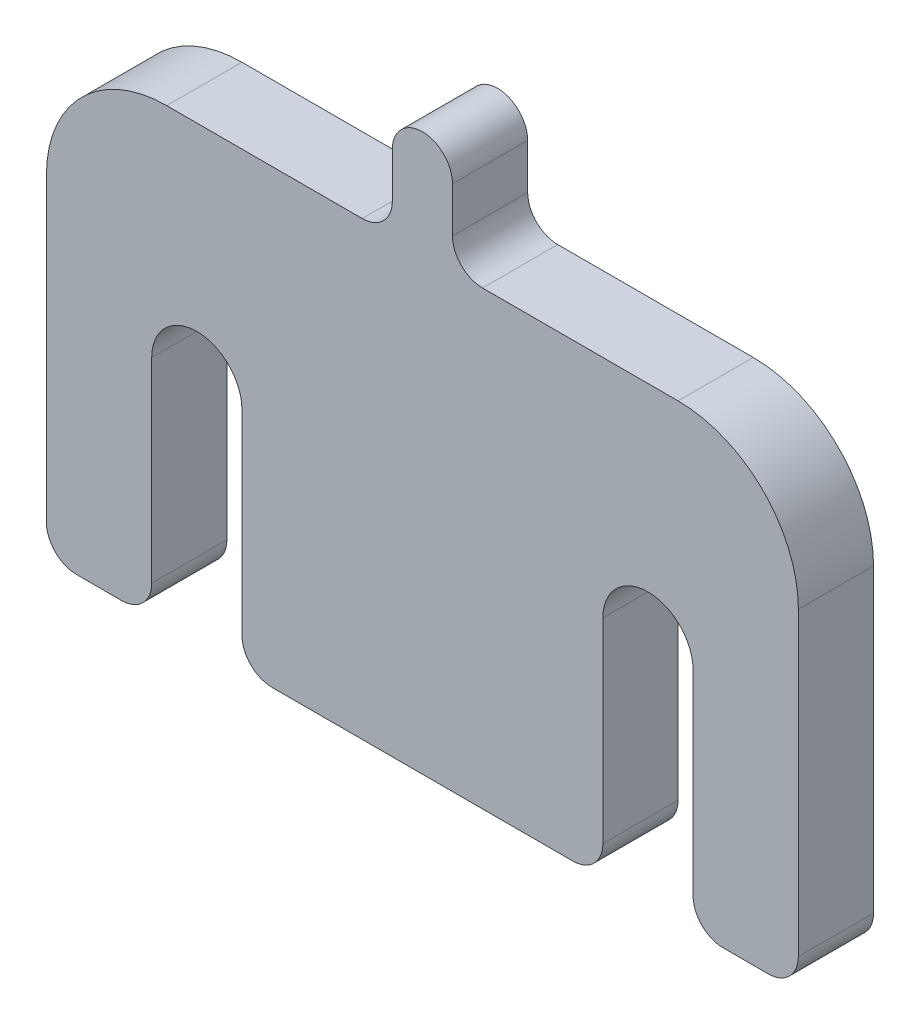
SolidWorks part; units mm, degrees
material "7075-O (SS)"
ref_plane "Płaszczyzna XY" through (0, 0, 0) normal (0, 0, 1) x (1, 0, 0)
ref_plane "Płaszczyzna XZ" through (0, 0, 0) normal (0, 1, 0) x (1, 0, 0)
ref_plane "Płaszczyzna YZ" through (0, 0, 0) normal (1, 0, 0) x (0, 0, -1)
sketch "Szkic1" plane through (0, 0, 0) normal (0, 0, 1) x (1, 0, 0)
  line L0 (15, 0) -> (-15, 0) construction
  line L1 (18, 0) -> (18, -15)
  line L2 (25, -15) -> (-25, -15)
  line L3 (25, -15) -> (25, 15)
  line L4 (25, 15) -> (-25, 15)
  line L5 (-25, -15) -> (-25, 15)
  line L6 (25, -15) -> (-25, 15) construction
  line L7 (25, 15) -> (-25, -15) construction
  line L8 (12, 0) -> (12, -15)
  line L9 (-12, 0) -> (-12, -15)
  line L10 (-18, 0) -> (-18, -15)
  line L11 (2, 20) -> (2, 15)
  line L12 (-2, 20) -> (-2, 15)
  line L13 (0, 20) -> (0, 0) construction
  arc A0 (-12, 0) -> (-18, 0) centre (-15, 0) ccw
  arc A1 (18, 0) -> (12, 0) centre (15, 0) ccw
  circle A2 centre (0, 20) radius 2
  point P1 (0, 0)
  point P6 (0, 0)
  dimension "D1" = 30
  dimension "D2" = 6
  dimension "D3" = 30
  dimension "D5" = 4
  dimension "D6" = 5
  dimension "D4" = 50
extrude "Dodanie-wyciągnięcie1" add sketch "Szkic1" along normal blind 5 contours A1 L1 L2 L3 L4 L5 L10 A0 L9 L8 | A2 L12 L4 L11 | A2
fillet "Zaokrąglenie1" radius 2 8 edges at (-25, -15, 2.5) (25, -15, 2.5) (-18, -15, 2.5) (-12, -15, 2.5) (12, -15, 2.5) (18, -15, 2.5) (-2, 15, 2.5) (2, 15, 2.5)
fillet "Zaokrąglenie2" radius 8 2 edges at (-25, 15, 2.5) (25, 15, 2.5)
